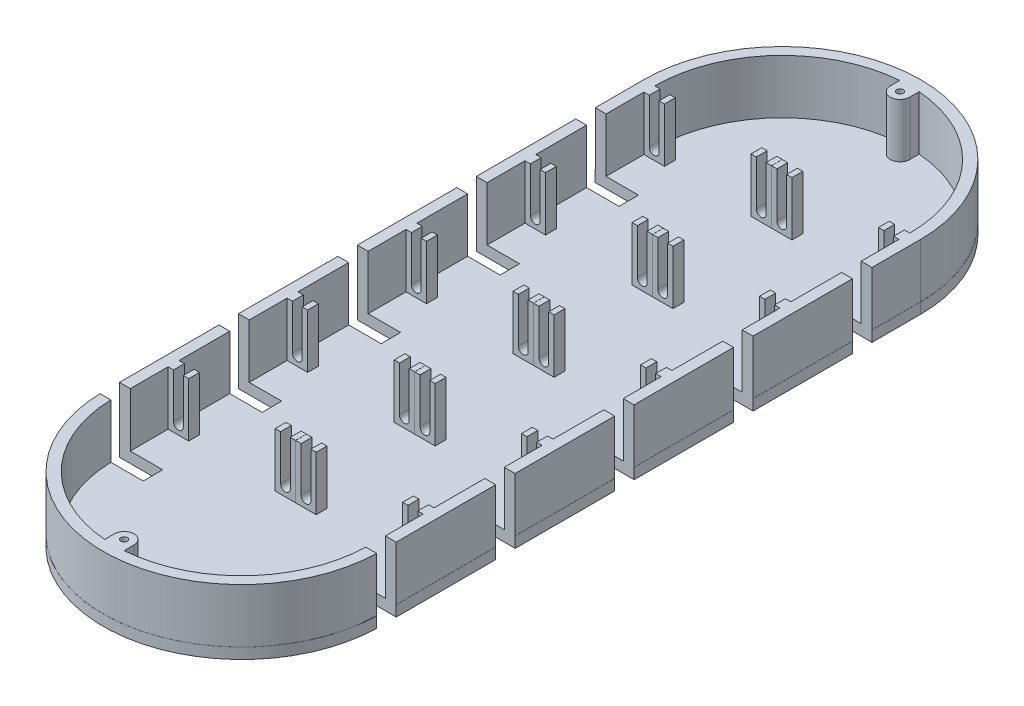
SolidWorks part; units mm, degrees
ref_plane "Front Plane" through (0, 0, 0) normal (0, 0, 1) x (1, 0, 0)
ref_plane "Top Plane" through (0, 0, 0) normal (0, 1, 0) x (1, 0, 0)
ref_plane "Right Plane" through (0, 0, 0) normal (1, 0, 0) x (0, 0, -1)
sketch "Sketch1" plane through (0, 0, 0) normal (0, 1, 0) x (1, 0, 0)
  line L0 (0, 0) -> (0, 250) construction
  line L1 (-64, 250) -> (-64, 0)
  line L2 (64, 250) -> (64, 0)
  arc A0 (-64, 0) -> (64, 0) centre (0, 0) ccw
  arc A1 (64, 250) -> (-64, 250) centre (0, 250) ccw
  dimension "D1" = 128
  dimension "D2" = 128
  dimension "D5" = 250
extrude "Boss-Extrude1" add sketch "Sketch1" along normal blind 5
sketch "Sketch2" plane through (0, 5, 0) normal (0, 1, 0) x (1, 0, 0)
  line L0 (-63.9742, 0) -> (-63.9742, 250)
  line L1 (63.9742, 250) -> (63.9742, 0)
  line L2 (-58.9742, 0) -> (-58.9742, 250)
  line L3 (58.9742, 250) -> (58.9742, 0)
  arc A0 (63.9742, 250) -> (-63.9742, 250) centre (0, 250) ccw
  arc A1 (-63.9742, 0) -> (63.9742, 0) centre (0, 0) ccw
  arc A2 (58.9742, 250) -> (-58.9742, 250) centre (0, 250) ccw
  arc A3 (-58.9742, 0) -> (58.9742, 0) centre (0, 0) ccw
  dimension "D1" = 5
extrude "Boss-Extrude2" add sketch "Sketch2" along normal blind 25
sketch "Sketch3" plane through (0, 5, 0) normal (0, 1, 0) x (1, 0, 0)
  line L0 (-49.4742, 195) -> (-9.4742, 195)
  line L2 (-58.9742, 0) -> (-58.9742, 25)
  line L3 (-58.9742, 250) -> (-58.9742, 0) construction
  line L5 (-49.4742, 250) -> (-9.4742, 250)
  line L7 (-58.9742, 25) -> (-58.9742, 55)
  line L8 (-58.9742, 250) -> (-58.9742, 0) construction
  line L9 (-58.9742, 55) -> (-58.9742, 80)
  line L10 (-58.9742, 80) -> (-58.9742, 110)
  line L11 (-58.9742, 110) -> (-58.9742, 135)
  line L12 (-58.9742, 135) -> (-58.9742, 165)
  line L13 (-58.9742, 165) -> (-58.9742, 190)
  line L14 (-58.9742, 190) -> (-58.9742, 220)
  line L15 (-58.9742, 220) -> (-58.9742, 245)
  line L16 (-58.9742, 245) -> (-58.9742, 275)
  line L17 (-58.9742, 25) -> (-58.9742, 30)
  line L18 (-58.9742, 30) -> (-49.4742, 30)
  line L19 (-49.4742, 30) -> (-49.4742, 25)
  line L20 (-49.4742, 25) -> (-58.9742, 25)
  line L21 (-49.4742, 30) -> (-9.4742, 30) construction
  line L22 (-49.4742, 85) -> (-9.4742, 85)
  line L23 (-9.4742, 30) -> (0.0258, 30)
  line L24 (-9.4742, 30) -> (-9.4742, 25)
  line L25 (-9.4742, 25) -> (0.0258, 25)
  line L26 (0.0258, 30) -> (0.0258, 25)
  line L27 (-58.9742, 80) -> (-49.4742, 80)
  line L28 (-58.9742, 80) -> (-58.9742, 85)
  line L29 (-58.9742, 85) -> (-49.4742, 85)
  line L30 (-49.4742, 80) -> (-49.4742, 85)
  line L31 (-49.4742, 140) -> (-9.4742, 140)
  line L32 (-9.4742, 85) -> (0.0258, 85)
  line L33 (-9.4742, 85) -> (-9.4742, 80)
  line L34 (-9.4742, 80) -> (0.0258, 80)
  line L35 (0.0258, 85) -> (0.0258, 80)
  line L36 (-58.9742, 135) -> (-49.4742, 135)
  line L37 (-58.9742, 135) -> (-58.9742, 140)
  line L38 (-58.9742, 140) -> (-49.4742, 140)
  line L39 (-49.4742, 135) -> (-49.4742, 140)
  line L40 (-58.9742, 190) -> (-49.4742, 190)
  line L41 (-9.4742, 140) -> (0.0258, 140)
  line L42 (-9.4742, 140) -> (-9.4742, 135)
  line L43 (-9.4742, 135) -> (0.0258, 135)
  line L44 (0.0258, 140) -> (0.0258, 135)
  line L46 (-58.9742, 190) -> (-58.9742, 195)
  line L53 (-58.9742, 245) -> (-49.4742, 245)
  line L54 (-58.9742, 245) -> (-58.9742, 250)
  line L55 (-58.9742, 250) -> (-49.4742, 250)
  line L56 (-49.4742, 245) -> (-49.4742, 250)
  line L57 (0, 0) -> (0, -47.7364) construction
  line L58 (-9.4742, 250) -> (0.0258, 250)
  line L59 (-9.4742, 250) -> (-9.4742, 245)
  line L60 (-9.4742, 245) -> (0.0258, 245)
  line L61 (0.0258, 250) -> (0.0258, 245)
  line L62 (9.4742, 245) -> (-0.0258, 245)
  line L63 (-0.0258, 250) -> (-0.0258, 245)
  line L64 (9.4742, 250) -> (-0.0258, 250)
  line L65 (9.4742, 250) -> (9.4742, 245)
  line L66 (58.9742, 250) -> (49.4742, 250)
  line L67 (49.4742, 245) -> (49.4742, 250)
  line L68 (58.9742, 245) -> (49.4742, 245)
  line L69 (58.9742, 245) -> (58.9742, 250)
  line L71 (58.9742, 195) -> (49.4742, 195)
  line L72 (49.4742, 190) -> (49.4742, 195)
  line L73 (58.9742, 190) -> (49.4742, 190)
  line L74 (58.9742, 190) -> (58.9742, 195)
  line L75 (9.4742, 135) -> (-0.0258, 135)
  line L76 (-0.0258, 140) -> (-0.0258, 135)
  line L77 (9.4742, 140) -> (-0.0258, 140)
  line L78 (9.4742, 140) -> (9.4742, 135)
  line L79 (58.9742, 140) -> (49.4742, 140)
  line L80 (49.4742, 135) -> (49.4742, 140)
  line L81 (58.9742, 135) -> (49.4742, 135)
  line L82 (58.9742, 135) -> (58.9742, 140)
  line L83 (58.9742, 85) -> (49.4742, 85)
  line L84 (49.4742, 80) -> (49.4742, 85)
  line L85 (58.9742, 80) -> (49.4742, 80)
  line L86 (58.9742, 80) -> (58.9742, 85)
  line L87 (9.4742, 80) -> (-0.0258, 80)
  line L88 (-0.0258, 85) -> (-0.0258, 80)
  line L89 (9.4742, 85) -> (-0.0258, 85)
  line L90 (9.4742, 85) -> (9.4742, 80)
  line L91 (9.4742, 25) -> (-0.0258, 25)
  line L92 (-0.0258, 30) -> (-0.0258, 25)
  line L93 (9.4742, 30) -> (-0.0258, 30)
  line L94 (9.4742, 30) -> (9.4742, 25)
  line L95 (49.4742, 25) -> (58.9742, 25)
  line L96 (49.4742, 30) -> (49.4742, 25)
  line L97 (58.9742, 30) -> (49.4742, 30)
  line L98 (58.9742, 25) -> (58.9742, 30)
  line L99 (-58.9742, 190) -> (-58.9742, 195)
  line L100 (-58.9742, 195) -> (-49.4742, 195)
  line L101 (-49.4742, 190) -> (-49.4742, 195)
  line L102 (58.9742, 195) -> (49.4742, 195)
  line L103 (-9.4742, 195) -> (0.0258, 195)
  line L104 (-9.4742, 195) -> (-9.4742, 190)
  line L105 (-9.4742, 190) -> (0.0258, 190)
  line L106 (0.0258, 195) -> (0.0258, 190)
  line L107 (49.4742, 190) -> (49.4742, 195)
  line L108 (58.9742, 190) -> (49.4742, 190)
  line L109 (58.9742, 190) -> (58.9742, 195)
  line L110 (9.4742, 190) -> (-0.0258, 190)
  line L111 (-0.0258, 195) -> (-0.0258, 190)
  line L112 (9.4742, 195) -> (-0.0258, 195)
  line L113 (9.4742, 195) -> (9.4742, 190)
  line L114 (0, 0) -> (-0.0258, 25)
  line L115 (0.0258, 30) -> (-0.0258, 80)
  line M19 (58.9742, 0) -> (58.9742, 250)
  dimension "D2" = 30
  dimension "D3" = 25
  dimension "D4" = 30
  dimension "D5" = 25
  dimension "D6" = 30
  dimension "D7" = 25
  dimension "D8" = 30
  dimension "D9" = 25
  dimension "D10" = 30
  dimension "D11" = 25
  dimension "D12" = 9.5
  dimension "D13" = 5
  dimension "D14" = 40
  dimension "D15" = 5
  dimension "D16" = 9.5
  dimension "D17" = 5
  dimension "D18" = 9.5
  dimension "D19" = 40
  dimension "D20" = 5
  dimension "D21" = 9.5
  dimension "D22" = 5
  dimension "D23" = 9.5
  dimension "D24" = 40
  dimension "D25" = 9.5
  dimension "D26" = 5
  dimension "D27" = 40
  dimension "D28" = 9.5
  dimension "D29" = 5
  dimension "D30" = 9.5
  dimension "D31" = 5
  dimension "D32" = 5
  dimension "D33" = 9.5
  dimension "D34" = 40
  dimension "D35" = 9.5
  dimension "D36" = 5
  dimension "D37" = 25
  dimension "D38" = 50
extrude "Boss-Extrude4" add sketch "Sketch3" along normal blind 25 contours L20 L19 L18 L7 | L92 L23 L24 L25 | L94 L93 L26 L91 | L97 L96 L95 M19 | L85 L83 L84 M19 | L90 L89 L35 L87 | L88 L32 L33 L34 | L27 L30 L29 L10 | L36 L39 L38 L12 | L76 L41 L42 L43 | L78 L77 L44 L75 | L81 L79 L80 M19 | L73 L71 L72 M19 | L113 L112 L106 L110 | L111 L103 L104 L105 | L40 L101 L100 L14 | L53 L56 L55 L16 | L63 L58 L59 L60 | L65 L64 L61 L62 | L68 L66 L67 M19
sketch "Sketch6" plane through (0, 0, -25) normal (0, 0, 1) x (1, 0, 0)
  line L0 (-54.2242, 30) -> (-54.2242, 9.9116) construction
  line L1 (-49.4742, 30) -> (-58.9742, 30) construction
  line L2 (-54.2242, 7) -> (-54.2242, 5)
  line L3 (-49.4742, 5) -> (-58.9742, 5) construction
  line L4 (-56.4742, 9.25) -> (-56.4742, 30)
  line L5 (-56.4742, 30) -> (-51.9742, 30)
  line L6 (-51.9742, 30) -> (-51.9742, 9.25)
  line L7 (-4.75, 30) -> (-4.75, 5) construction
  line L8 (-9.4742, 30) -> (-0.0258, 30) construction
  line L9 (-9.4742, 5) -> (-0.0258, 5) construction
  line L10 (-4.75, 7) -> (-4.75, 5)
  line L11 (-7, 9.25) -> (-7, 30)
  line L12 (-7, 30) -> (-2.5, 30)
  line L13 (-2.5, 30) -> (-2.5, 9.25)
  line L15 (4.75, 30) -> (4.75, 5) construction
  line L16 (9.4742, 30) -> (0.0258, 30) construction
  line L17 (9.4742, 5) -> (0.0258, 5) construction
  line L19 (4.75, 7) -> (4.75, 5)
  line L20 (2.5, 9.25) -> (2.5, 30)
  line L21 (2.5, 30) -> (7, 30)
  line L22 (7, 30) -> (7, 9.25)
  line L23 (54.2242, 30) -> (54.2242, 5) construction
  line L24 (49.4742, 30) -> (58.9742, 30) construction
  line L25 (49.4742, 5) -> (58.9742, 5) construction
  line L26 (54.2242, 7) -> (54.2242, 5)
  line L27 (51.9742, 9.25) -> (51.9742, 30)
  line L28 (51.9742, 30) -> (56.4742, 30)
  line L29 (56.4742, 30) -> (56.4742, 9.25)
  circle A0 centre (-54.2242, 9.25) radius 2.25
  circle A1 centre (-4.75, 9.25) radius 2.25
  circle A2 centre (4.75, 9.25) radius 2.25
  circle A3 centre (54.2242, 9.25) radius 2.25
  line M12 (-49.4742, 30) -> (-58.9742, 30)
  dimension "D1" = 4.5
  dimension "D3" = 4.5
  dimension "D5" = 4.5
  dimension "D7" = 4.5
  dimension "D2" = 2
  dimension "D4" = 2
  dimension "D6" = 2
  dimension "D8" = 2
extrude "Cut-Extrude3" cut sketch "Sketch6" against normal blind 228 contours A0 L6 L4 M12 | A1 | A1 L13 L12 L11 | A2 L22 L21 L20 | A3 L29 L28 L27
sketch "Sketch7" plane through (0, 5, 0) normal (0, 1, 0) x (1, 0, 0)
  line L0 (58.9742, 62.5) -> (58.9742, 53.5)
  line L1 (63.9742, 62.5) -> (63.9742, 53.5)
  line L9 (64, 0) -> (64, 250) construction
  line L10 (64, -1.5) -> (57.6775, -1.5)
  line L11 (64, -1.5) -> (64, 7.5)
  line L12 (64, 7.5) -> (57.6775, 7.5)
  line L13 (57.6775, -1.5) -> (57.6775, 7.5)
  line L14 (58.9742, 30) -> (58.9742, 80) construction
  line L15 (63.9742, 0) -> (63.9742, 250) construction
  line L20 (58.9742, 62.5) -> (63.9742, 62.5)
  line L21 (58.9742, 85) -> (58.9742, 135) construction
  line L22 (58.9742, 62.5) -> (58.9742, 53.5)
  line L23 (58.9742, 108.5) -> (63.9742, 108.5)
  line L25 (58.9742, 117.5) -> (63.9742, 117.5)
  line L26 (63.9742, 108.5) -> (63.9742, 117.5)
  line L27 (58.9742, 53.5) -> (63.9742, 53.5)
  line L29 (58.9742, 62.5) -> (63.9742, 62.5)
  line L30 (63.9742, 53.5) -> (63.9742, 62.5)
  line L31 (58.9742, 140) -> (58.9742, 190) construction
  line L32 (58.9742, 53.5) -> (63.9742, 53.5)
  line L33 (58.9742, 163.5) -> (63.9742, 163.5)
  line L35 (58.9742, 172.5) -> (63.9742, 172.5)
  line L36 (63.9742, 163.5) -> (63.9742, 172.5)
  line L37 (58.9742, 195) -> (58.9742, 245) construction
  line L38 (0, -58.9742) -> (0, -6.3721) construction
  line L39 (58.9742, 218.5) -> (64, 218.5)
  line L41 (58.9742, 227.5) -> (64, 227.5)
  line L42 (64, 218.5) -> (64, 227.5)
  line L43 (-57.6775, -1.5) -> (-57.6775, 7.5)
  line L44 (-64, -1.5) -> (-57.6775, -1.5)
  line L45 (-64, 25) -> (-64, -1.5) construction
  line L46 (-64, 7.5) -> (-57.6775, 7.5)
  line L47 (-58.9742, 80) -> (-58.9742, 53.5) construction
  line L48 (-58.9742, 53.5) -> (-63.9742, 53.5)
  line L49 (-63.9742, 53.5) -> (-63.9742, 62.5)
  line L50 (-58.9742, 62.5) -> (-63.9742, 62.5)
  line L51 (-63.9742, 108.5) -> (-63.9742, 117.5)
  line L52 (-58.9742, 108.5) -> (-63.9742, 108.5)
  line L53 (-58.9742, 135) -> (-58.9742, 108.5) construction
  line L54 (-58.9742, 117.5) -> (-63.9742, 117.5)
  line L55 (-58.9742, 190) -> (-58.9742, 163.5) construction
  line L56 (-58.9742, 163.5) -> (-63.9742, 163.5)
  line L57 (-63.9742, 163.5) -> (-63.9742, 172.5)
  line L58 (-58.9742, 172.5) -> (-63.9742, 172.5)
  line L59 (-58.9742, 245) -> (-58.9742, 218.5) construction
  line L60 (-58.9742, 218.5) -> (-64, 218.5)
  line L61 (-64, 218.5) -> (-64, 227.5)
  line L62 (-58.9742, 227.5) -> (-64, 227.5)
  line L63 (-58.9742, 227.5) -> (-58.9742, 218.5)
  line L64 (-58.9742, 172.5) -> (-58.9742, 163.5)
  line L65 (-58.9742, 117.5) -> (-58.9742, 108.5)
  line L66 (-58.9742, 62.5) -> (-58.9742, 53.5)
  line L67 (-64, 7.5) -> (-64, -1.5)
  line L68 (63.9742, 62.5) -> (63.9742, 53.5)
  line L69 (58.9742, 117.5) -> (63.9742, 117.5)
  line L70 (58.9742, 117.5) -> (58.9742, 108.5)
  line L71 (58.9742, 108.5) -> (63.9742, 108.5)
  line L76 (63.9742, 117.5) -> (63.9742, 108.5)
  line L77 (58.9742, 172.5) -> (63.9742, 172.5)
  line L78 (58.9742, 172.5) -> (58.9742, 163.5)
  line L79 (58.9742, 163.5) -> (63.9742, 163.5)
  line L80 (63.9742, 172.5) -> (63.9742, 163.5)
  line L81 (58.9742, 227.5) -> (64, 227.5)
  line L82 (58.9742, 227.5) -> (58.9742, 218.5)
  line L83 (58.9742, 218.5) -> (64, 218.5)
  line L84 (64, 227.5) -> (64, 218.5)
  arc A0 (-58.9742, 0) -> (58.9742, 0) centre (0, 0) ccw construction
  dimension "D2" = 9
  dimension "D4" = 9
  dimension "D6" = 9
  dimension "D8" = 9
  dimension "D10" = 9
extrude "Cut-Extrude7" cut sketch "Sketch7" along normal blind 32 contours L66 L50 L49 L48 | L64 L58 L57 L56 | L41 L82 L39 L42 | L35 L78 L33 L36 | L25 L70 L23 L26 | L0 L27 L1 L20 | L13 L10 L11 L12 | L46 L43 L44 L67 | L54 L51 L52 L65 | L62 L61 L60 L63
sketch "Sketch8" plane through (0, 5, 0) normal (0, 1, 0) x (1, 0, 0)
  line L0 (0, 0) -> (0, -19.0299) construction
  line L1 (-63.9742, 227.5) -> (-43.9742, 227.5)
  line L2 (-63.9742, 227.5) -> (-63.9742, 218.5)
  line L3 (-63.9742, 218.5) -> (-43.9742, 218.5)
  line L4 (-43.9742, 227.5) -> (-43.9742, 218.5)
  line L5 (-63.9742, 172.5) -> (-43.9742, 172.5)
  line L6 (-63.9742, 172.5) -> (-63.9742, 163.5)
  line L7 (-63.9742, 163.5) -> (-43.9742, 163.5)
  line L8 (-43.9742, 172.5) -> (-43.9742, 163.5)
  line L9 (-63.9742, 117.5) -> (-43.9742, 117.5)
  line L10 (-63.9742, 117.5) -> (-63.9742, 108.5)
  line L11 (-63.9742, 108.5) -> (-43.9742, 108.5)
  line L12 (-43.9742, 117.5) -> (-43.9742, 108.5)
  line L13 (-63.9742, 62.5) -> (-43.9742, 62.5)
  line L14 (-63.9742, 62.5) -> (-63.9742, 53.5)
  line L15 (-63.9742, 53.5) -> (-43.9742, 53.5)
  line L16 (-43.9742, 62.5) -> (-43.9742, 53.5)
  line L17 (-63.9742, 7.5) -> (-43.9742, 7.5)
  line L18 (-63.9742, 7.5) -> (-63.9742, -1.5)
  line L19 (-63.9742, -1.5) -> (-43.9742, -1.5)
  line L20 (-43.9742, 7.5) -> (-43.9742, -1.5)
  line L21 (63.9742, -1.5) -> (43.9742, -1.5)
  line L22 (-63.9742, 227.5) -> (-71.7521, 227.5)
  line L23 (-63.9742, 227.5) -> (-63.9742, 218.5)
  line L24 (-63.9742, 218.5) -> (-71.7521, 218.5)
  line L25 (-71.7521, 227.5) -> (-71.7521, 218.5)
  line L26 (-63.9742, 172.5) -> (-75.0729, 172.5)
  line L27 (-63.9742, 172.5) -> (-63.9742, 163.5)
  line L28 (-63.9742, 163.5) -> (-75.0729, 163.5)
  line L29 (-75.0729, 172.5) -> (-75.0729, 163.5)
  line L30 (-63.9742, 117.5) -> (-77.6852, 117.5)
  line L31 (-63.9742, 117.5) -> (-63.9742, 108.5)
  line L32 (-63.9742, 108.5) -> (-77.6852, 108.5)
  line L33 (-77.6852, 117.5) -> (-77.6852, 108.5)
  line L34 (-63.9742, 62.5) -> (-75.0729, 62.5)
  line L35 (-63.9742, 62.5) -> (-63.9742, 53.5)
  line L36 (-63.9742, 53.5) -> (-75.0729, 53.5)
  line L37 (-75.0729, 62.5) -> (-75.0729, 53.5)
  line L38 (-63.9742, 7.5) -> (-75.0729, 7.5)
  line L39 (-63.9742, 7.5) -> (-63.9742, -1.5)
  line L40 (-63.9742, -1.5) -> (-75.0729, -1.5)
  line L41 (-75.0729, 7.5) -> (-75.0729, -1.5)
  line L42 (43.9742, 7.5) -> (43.9742, -1.5)
  line L43 (63.9742, 7.5) -> (43.9742, 7.5)
  line L44 (63.9742, 7.5) -> (63.9742, -1.5)
  line L45 (63.9742, -1.5) -> (75.0729, -1.5)
  line L46 (75.0729, 7.5) -> (75.0729, -1.5)
  line L47 (63.9742, 7.5) -> (75.0729, 7.5)
  line L48 (63.9742, 7.5) -> (63.9742, -1.5)
  line L49 (63.9742, 53.5) -> (43.9742, 53.5)
  line L50 (43.9742, 62.5) -> (43.9742, 53.5)
  line L51 (63.9742, 62.5) -> (43.9742, 62.5)
  line L52 (63.9742, 62.5) -> (63.9742, 53.5)
  line L53 (63.9742, 53.5) -> (75.0729, 53.5)
  line L54 (75.0729, 62.5) -> (75.0729, 53.5)
  line L55 (63.9742, 62.5) -> (75.0729, 62.5)
  line L56 (63.9742, 62.5) -> (63.9742, 53.5)
  line L57 (63.9742, 108.5) -> (43.9742, 108.5)
  line L58 (43.9742, 117.5) -> (43.9742, 108.5)
  line L59 (63.9742, 117.5) -> (43.9742, 117.5)
  line L60 (63.9742, 117.5) -> (63.9742, 108.5)
  line L61 (63.9742, 108.5) -> (77.6852, 108.5)
  line L62 (77.6852, 117.5) -> (77.6852, 108.5)
  line L63 (63.9742, 117.5) -> (77.6852, 117.5)
  line L64 (63.9742, 117.5) -> (63.9742, 108.5)
  line L65 (63.9742, 163.5) -> (43.9742, 163.5)
  line L66 (43.9742, 172.5) -> (43.9742, 163.5)
  line L67 (63.9742, 172.5) -> (43.9742, 172.5)
  line L68 (63.9742, 172.5) -> (63.9742, 163.5)
  line L69 (63.9742, 163.5) -> (75.0729, 163.5)
  line L70 (75.0729, 172.5) -> (75.0729, 163.5)
  line L71 (63.9742, 172.5) -> (75.0729, 172.5)
  line L72 (63.9742, 172.5) -> (63.9742, 163.5)
  line L73 (63.9742, 218.5) -> (43.9742, 218.5)
  line L74 (43.9742, 227.5) -> (43.9742, 218.5)
  line L75 (63.9742, 227.5) -> (43.9742, 227.5)
  line L76 (63.9742, 227.5) -> (63.9742, 218.5)
  line L77 (63.9742, 218.5) -> (71.7521, 218.5)
  line L78 (71.7521, 227.5) -> (71.7521, 218.5)
  line L79 (63.9742, 227.5) -> (71.7521, 227.5)
  line L80 (63.9742, 227.5) -> (63.9742, 218.5)
  dimension "D1" = 9
  dimension "D2" = 20
  dimension "D3" = 9
  dimension "D4" = 20
  dimension "D5" = 9
  dimension "D6" = 20
  dimension "D7" = 9
  dimension "D8" = 20
  dimension "D9" = 9
  dimension "D10" = 20
extrude "Cut-Extrude9" cut sketch "Sketch8" against normal blind 17 contours L22 L25 L24 L2 | L4 L1 L2 L3 | L26 L29 L28 L6 | L8 L5 L6 L7 | L30 L33 L32 L10 | L12 L9 L10 L11 | L34 L37 L36 L14 | L16 L13 L14 L15 | L38 L41 L40 L18 | L20 L17 L18 L19 | L44 L43 L42 L21 | L47 L44 L45 L46 | L55 L52 L53 L54 | L52 L51 L50 L49 | L63 L60 L61 L62 | L60 L59 L58 L57 | L71 L68 L69 L70 | L68 L67 L66 L65 | L79 L76 L77 L78 | L76 L75 L74 L73
sketch "Sketch9" plane through (0, 5, 0) normal (0, 1, 0) x (1, 0, 0)
  line L0 (0, 313.9742) -> (0, -63.9742) construction
  line L1 (0, -58.8023) -> (-4.5, -58.8023)
  line L2 (-4.5, -58.8023) -> (-4.5, -54.3023)
  line L3 (4.5, -54.3023) -> (4.5, -57.8658)
  line L4 (0, -58.8023) -> (4.5, -58.8023)
  line L5 (4.5, -57.8658) -> (4.5, -58.8023)
  line L6 (0, 308.9568) -> (-4.5, 308.9568)
  line L7 (-4.5, 308.9568) -> (-4.4924, 304.1946)
  line L8 (0, 308.9568) -> (4.5, 308.9568)
  line L9 (4.5, 308.9568) -> (4.5, 304.4568)
  line L11 (-4.5, -58.8023) -> (4.5, -58.8023)
  line L12 (-4.5, -58.8023) -> (-4.5, -59.7681)
  line L13 (-4.5, -59.7681) -> (4.5, -59.7681)
  line L14 (4.5, -58.8023) -> (4.5, -59.7681)
  line L15 (-4.5, 308.9568) -> (4.5, 308.9568)
  line L16 (-4.5, 308.9568) -> (-4.5, 310.348)
  line L17 (-4.5, 310.348) -> (4.5, 310.348)
  line L18 (4.5, 308.9568) -> (4.5, 310.348)
  arc A0 (63.9742, 250) -> (-63.9742, 250) centre (0, 250) ccw construction
  arc A1 (-63.9566, -1.5) -> (63.9566, -1.5) centre (0, 0) ccw construction
  circle A2 centre (0, 304.4568) radius 1.5
  circle A3 centre (0, -54.3023) radius 1.5
  circle A4 centre (0, 304.4568) radius 4.5
  circle A5 centre (0, -54.3023) radius 4.5
  arc A6 (-58.9551, -1.5) -> (58.9551, -1.5) centre (0, 0) ccw construction
  arc A7 (-58.9551, -1.5) -> (58.9551, -1.5) centre (0, 0) ccw construction
  dimension "D1" = 3
  dimension "D2" = 3
  dimension "D3" = 3
  dimension "D4" = 3
extrude "Boss-Extrude10" add sketch "Sketch9" along normal blind 25 contours L0 A4 L7 A2 | A4 L0 A2 | A4 L9 L8 | A4 L6 L7 | L0 L17 L16 L6 | L17 L0 L8 L18 | L0 L1 L12 L13 | A5 L2 L1 | L0 A5 A3 | A5 L0 A3 | A5 L4 L5 L3 | L4 L0 L13 L14
